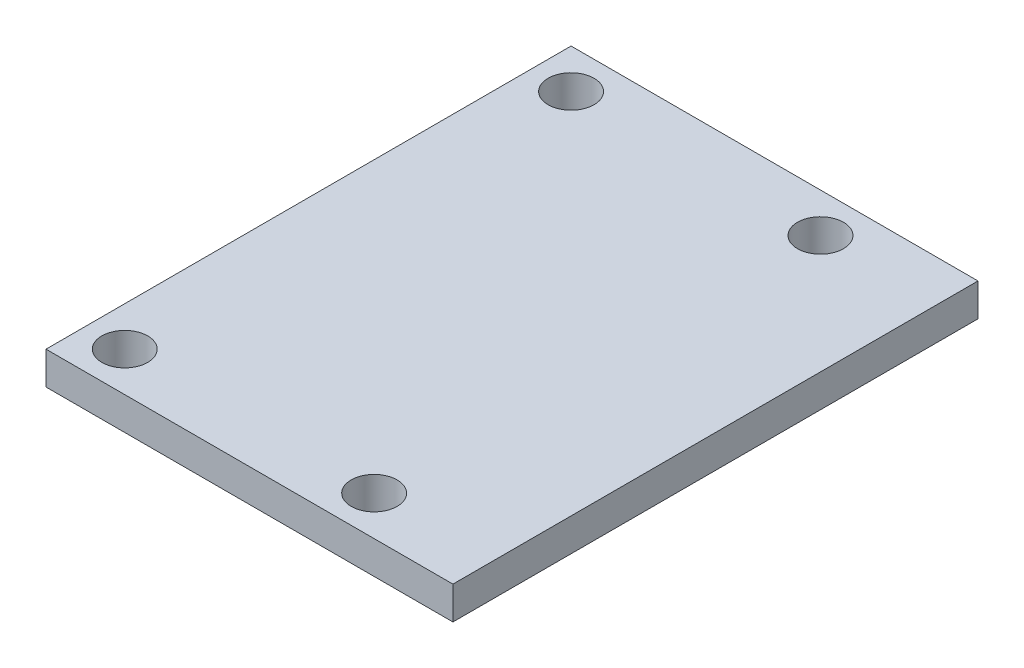
SolidWorks part; units mm, degrees
ref_plane "Front Plane" through (0, 0, 0) normal (0, 0, 1) x (1, 0, 0)
ref_plane "Top Plane" through (0, 0, 0) normal (0, 1, 0) x (1, 0, 0)
ref_plane "Right Plane" through (0, 0, 0) normal (1, 0, 0) x (0, 0, -1)
sketch "Sketch1" plane through (0, 0, 0) normal (0, 0, 1) x (1, 0, 0)
  line L1 (0, 0) -> (-31, 0)
  line L2 (-6, 2.5) -> (0, 2.5)
  line L3 (-6, 2.5) -> (-31, 2.5)
  line L4 (-31, 0) -> (-31, 2.5)
  line L5 (0, 2.5) -> (0, 0)
  point P0 (0, 0)
  dimension "D1" = 2.5
  dimension "D2" = 31
extrude "Boss-Extrude1" add sketch "Sketch1" along normal blind 40
sketch "Sketch3" plane through (0, 2.5, 0) normal (0, 1, 0) x (1, 0, 0)
  line L0 (-9, -3) -> (-6, -3) construction
  line L1 (-6, -40) -> (-6, 0) construction
  line L2 (-6, 0) -> (-31, 0) construction
  line L3 (-9, -3) -> (-9, 0) construction
  line L4 (-28, -3) -> (-28, 0) construction
  line L5 (-28, -37) -> (-28, -40) construction
  line L6 (0, -40) -> (-31, -40) construction
  line L7 (-28, -3) -> (-31, -3) construction
  line L8 (-31, -40) -> (-31, 0) construction
  line L9 (-28, -37) -> (-31, -37) construction
  line L10 (-6, -37) -> (-9, -37) construction
  line L11 (-9, -37) -> (-9, -40) construction
  circle A0 centre (-9, -3) radius 1.75
  circle A1 centre (-28, -3) radius 1.75
  circle A2 centre (-28, -37) radius 1.75
  circle A3 centre (-9, -37) radius 1.75
  dimension "D2" = 3.5
  dimension "D3" = 3
extrude "Cut-Extrude2" cut sketch "Sketch3" against normal up to next
